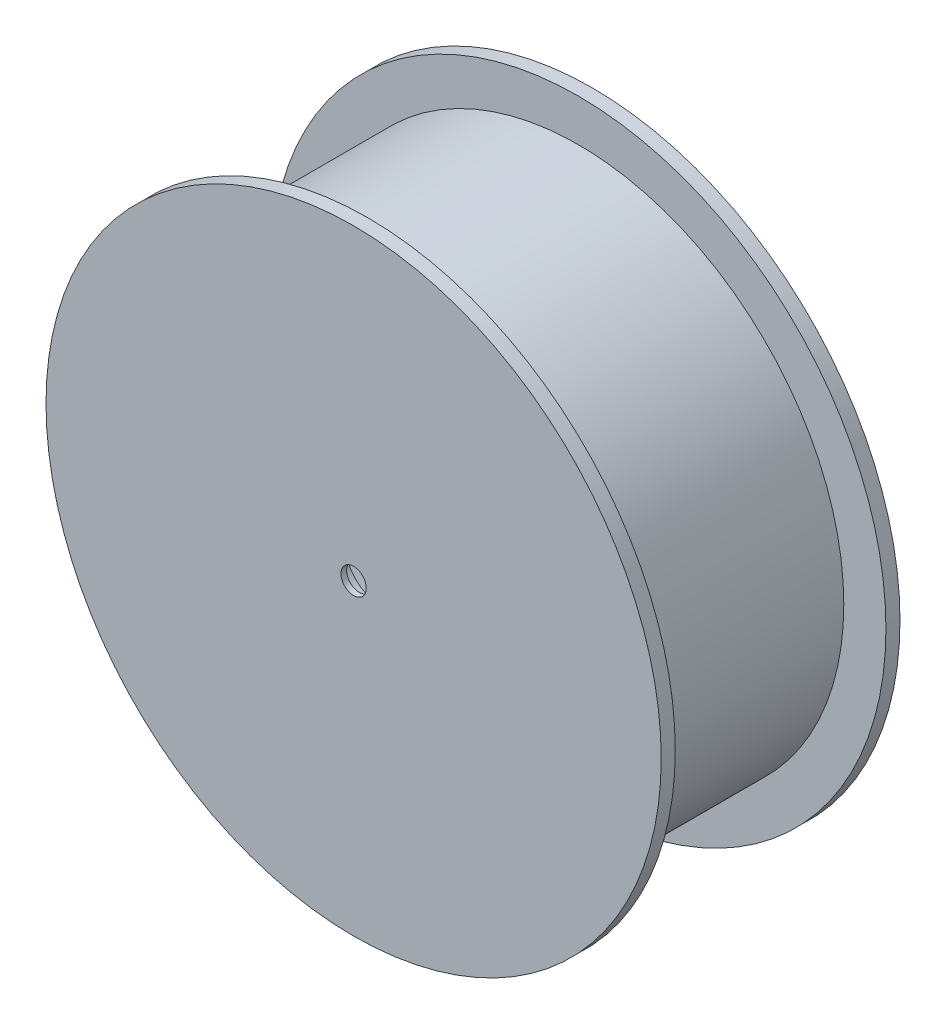
SolidWorks part; units mm, degrees
ref_plane "Front Plane" through (0, 0, 0) normal (0, 0, 1) x (1, 0, 0)
ref_plane "Top Plane" through (0, 0, 0) normal (0, 1, 0) x (1, 0, 0)
ref_plane "Right Plane" through (0, 0, 0) normal (1, 0, 0) x (0, 0, -1)
sketch "Sketch3" plane through (0, 0, 0) normal (1, 0, 0) x (0, 0, -1)
  line L0 (-33.8971, 0) -> (49.0441, 0) construction
  line L1 (-24.4118, 0) -> (-24.4118, -109.5)
  line L2 (-24.4118, -109.5) -> (-19.4118, -109.5)
  line L3 (60.5882, -84.5) -> (60.5882, -109.5)
  line L4 (55.5882, -94.5) -> (55.5882, -109.5)
  line L5 (-24.4118, 0) -> (-14.4118, 0)
  line L6 (-14.4118, 0) -> (-14.4118, -84.5)
  line L7 (-14.4118, -84.5) -> (60.5882, -84.5)
  line L8 (-19.4118, -109.5) -> (-19.4118, -94.5)
  line L9 (-19.4118, -94.5) -> (55.5882, -94.5)
  line L10 (55.5882, -109.5) -> (60.5882, -109.5)
  dimension "D2" = 84.5
  dimension "D3" = 94.5
  dimension "D1" = 109.5
  dimension "D5" = 109.5
  dimension "D7" = 5
  dimension "D4" = 75
  dimension "D6" = 10
  dimension "D8" = 5
revolve "Revolve1" add sketch "Sketch3" angle 360 about L0
sketch "Sketch5" plane through (0, 0, 24.4118) normal (0, 0, 1) x (1, 0, 0)
  circle A0 centre (0, 0) radius 4.5
  dimension "D1" = 9
extrude "Cut-Extrude1" cut sketch "Sketch5" against normal through all
sketch "Sketch6" plane through (0, 0, 14.4118) normal (0, 0, -1) x (-1, 0, 0)
  circle A0 centre (0, 0) radius 13
  dimension "D1" = 26
extrude "Cut-Extrude2" cut sketch "Sketch6" against normal blind 8
sketch "Sketch8" plane through (0, 0, -60.5882) normal (0, 0, -1) x (-1, 0, 0)
  line L0 (0, 0) -> (0, 112.5043) construction
  arc A0 (11.9697, 83.6479) -> (-11.9697, 83.6479) centre (0, 84.5) ccw
  circle A1 centre (0, 0) radius 84.5 construction
  arc A2 (11.9697, 83.6479) -> (-11.9697, 83.6479) centre (0, 0) ccw
  arc A3 (78.4261, 31.4579) -> (66.4564, 52.19) centre (73.1791, 42.25) ccw
  arc A4 (78.4261, 31.4579) -> (66.4564, 52.19) centre (0, 0) ccw
  arc A5 (66.4564, -52.19) -> (78.4261, -31.4579) centre (73.1791, -42.25) ccw
  arc A6 (66.4564, -52.19) -> (78.4261, -31.4579) centre (0, 0) ccw
  arc A7 (-11.9697, -83.6479) -> (11.9697, -83.6479) centre (0, -84.5) ccw
  arc A8 (-11.9697, -83.6479) -> (11.9697, -83.6479) centre (0, 0) ccw
  arc A9 (-78.4261, -31.4579) -> (-66.4564, -52.19) centre (-73.1791, -42.25) ccw
  arc A10 (-78.4261, -31.4579) -> (-66.4564, -52.19) centre (0, 0) ccw
  arc A11 (-66.4564, 52.19) -> (-78.4261, 31.4579) centre (-73.1791, 42.25) ccw
  arc A12 (-66.4564, 52.19) -> (-78.4261, 31.4579) centre (0, 0) ccw
  point P25 (0, 0)
  dimension "D1" = 24
  dimension "D2" = 6
extrude "Cut-Extrude4" cut sketch "Sketch8" against normal blind 3
sketch "Sketch9" plane through (0, 0, -57.5882) normal (0, 0, -1) x (-1, 0, 0)
  line L0 (0, 84.5) -> (0, 96.5) construction
  arc A0 (11.9697, 83.6479) -> (-11.9697, 83.6479) centre (0, 0) ccw construction
  arc A1 (11.9697, 83.6479) -> (-11.9697, 83.6479) centre (0, 84.5) ccw construction
  circle A2 centre (0, 90.5) radius 1
  circle A3 centre (78.3753, 45.25) radius 1
  circle A4 centre (78.3753, -45.25) radius 1
  circle A5 centre (0, -90.5) radius 1
  circle A6 centre (-78.3753, -45.25) radius 1
  circle A7 centre (-78.3753, 45.25) radius 1
  point P10 (0, 0)
  point P23 (0, 0)
  dimension "D1" = 2
  dimension "D2" = 6
extrude "Cut-Extrude5" cut sketch "Sketch9" against normal blind 5
equation "\"inner_r\"= 169 / 2"
equation "\"D2@Sketch3\"=\"inner_r\""
equation "\"hub_depth\"=55"
equation "\"flange_r\"=40.5044"
equation "\"D3@Sketch3\"=\"inner_r\"+10"
equation "\"D1@Sketch3\"=\"inner_r\"+25"
equation "\"D5@Sketch3\"=\"inner_r\"+25"
